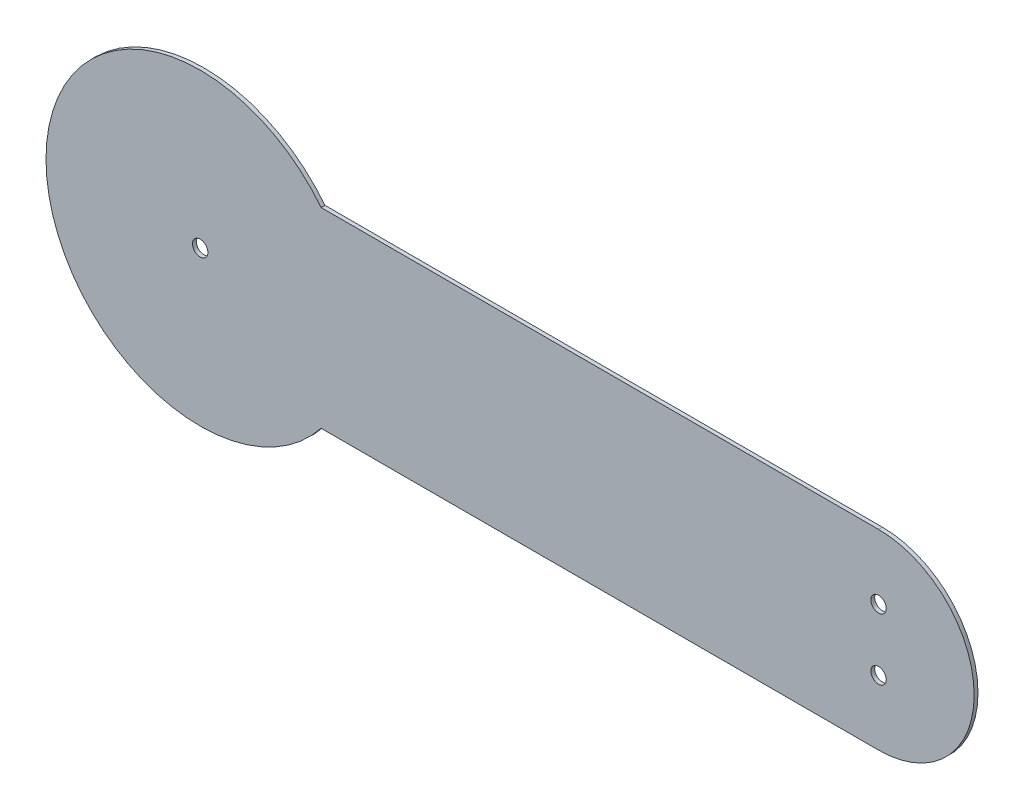
SolidWorks part; units mm, degrees
ref_plane "Front Plane" through (0, 0, 0) normal (0, 0, 1) x (1, 0, 0)
ref_plane "Top Plane" through (0, 0, 0) normal (0, 1, 0) x (1, 0, 0)
ref_plane "Right Plane" through (0, 0, 0) normal (1, 0, 0) x (0, 0, -1)
sketch "Sketch1" plane through (0, 0, 0) normal (0, 0, 1) x (1, 0, 0)
  line L0 (0, 0) -> (279.4, 0) construction
  line L1 (279.4, 42.545) -> (51.3369, 42.545) construction
  line L2 (51.3369, -42.545) -> (279.4, -42.545) construction
  line L3 (279.4, -39.37) -> (49.8222, -39.37)
  line L4 (279.4, 39.37) -> (49.8222, 39.37)
  line L5 (279.4, -12.7) -> (279.4, 12.7) construction
  arc A0 (51.3369, 42.545) -> (51.3369, -42.545) centre (0, 0) ccw construction
  arc A1 (279.4, -42.545) -> (279.4, 42.545) centre (279.4, 0) ccw construction
  arc A2 (49.8222, 39.37) -> (49.8222, -39.37) centre (0, 0) ccw
  arc A3 (279.4, -39.37) -> (279.4, 39.37) centre (279.4, 0) ccw
  circle A4 centre (0, 0) radius 3.175
  circle A5 centre (279.4, 12.7) radius 3.175
  circle A6 centre (279.4, -12.7) radius 3.175
  dimension "D1" = 127
  dimension "D2" = 3.175
  dimension "D3" = 39.37
  dimension "D4" = 3.175
  dimension "D6" = 6.35
  dimension "D7" = 6.35
  dimension "D8" = 6.35
  dimension "D5" = 279.4
  dimension "D9" = 25.4
extrude "Boss-Extrude1" add sketch "Sketch1" along normal blind 1.5875
equation "\"D3@Sketch1\"=3.35/2 - .125"
